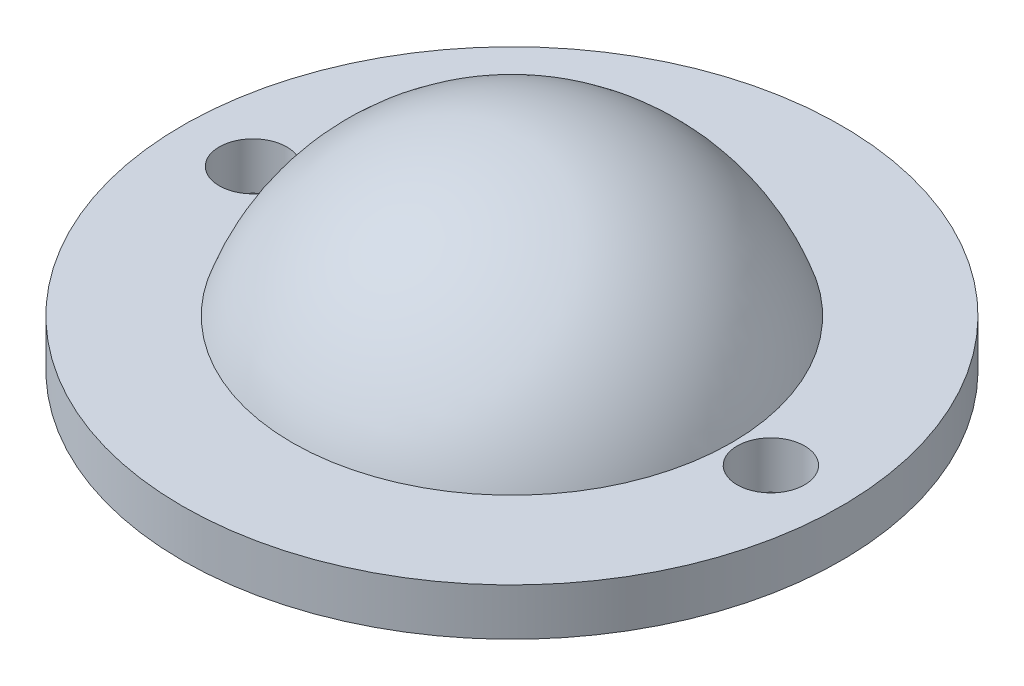
SolidWorks part; units mm, degrees
material "1060 Alloy"
ref_plane "Front Plane" through (0, 0, 0) normal (0, 0, 1) x (1, 0, 0)
ref_plane "Top Plane" through (0, 0, 0) normal (0, 1, 0) x (1, 0, 0)
ref_plane "Right Plane" through (0, 0, 0) normal (1, 0, 0) x (0, 0, -1)
sketch "Sketch3" plane through (0, 0, 0) normal (1, 0, 0) x (0, 0, -1)
  line L0 (0, 0) -> (0, 13) construction
  line L1 (0, 0) -> (21, 0) construction
  line L2 (21, 0) -> (21, 3)
  line L3 (21, 3) -> (14, 3)
  line L4 (0, 13) -> (10.4801, 13) construction
  line L5 (21, 0) -> (11, 0)
  line L6 (0, 0) -> (0, -2) construction
  line L7 (0, -2) -> (16.1412, -2) construction
  line L8 (0, 13) -> (0, -2)
  arc A0 (0, 13) -> (14, 3) centre (0, -1.8) cw
  arc A1 (0, -2) -> (11, 0) centre (0, 29.25) ccw
  dimension "D1" = 3
  dimension "D2" = 42
  dimension "D3" = 10
  dimension "D4" = 28
  dimension "D5" = 2
  dimension "D6" = 22
revolve "Revolve1" add sketch "Sketch3" angle 360 about L8
sketch "Sketch4" plane through (0, 0, 0) normal (1, 0, 0) x (0, 0, -1)
  line L0 (0, 0) -> (0, -7) construction
  line L1 (21, 3) -> (14, 3) construction
  line L2 (0, 13) -> (0, -2) construction
  line L3 (0, -7) -> (0, 8)
  arc A1 (0, -7) -> (0, 8) centre (0, 0.5) ccw
  point P6 (0, 8)
  point P9 (0, -11.0202)
  point P11 (0, -7)
  dimension "D2" = 7.5
  dimension "D1" = 10
revolve "Revolve3" add sketch "Sketch4" angle 360 about L0
sketch "Sketch6" plane through (0, 3, 0) normal (0, 1, 0) x (1, 0, 0)
  circle A0 centre (16.5, 0) radius 2.15
  circle A1 centre (-16.5, 0) radius 2.15
  point P7 (0, 0)
  dimension "D1" = 4.3
  dimension "D2" = 16.5
  dimension "D3" = 2
extrude "Cut-Extrude1" cut sketch "Sketch6" against normal through all
sketch "Sketch7" plane through (0, 0, 0) normal (1, 0, 0) x (0, 0, -1)
  circle A0 centre (0, 0.5) radius 7.5 construction
  point P0 (0, -7)
  point P1 (0, 0)
